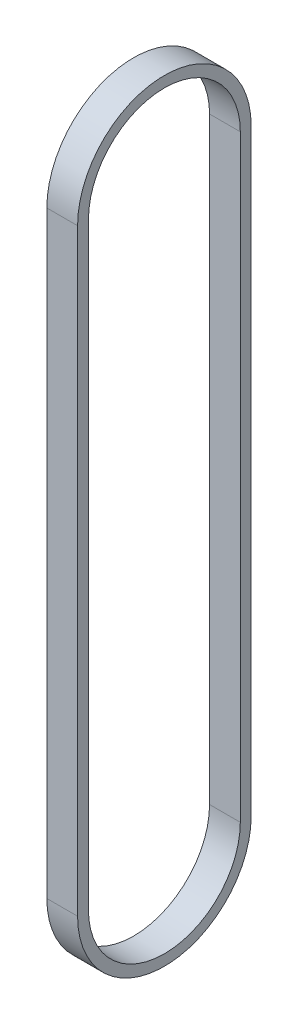
SolidWorks part; units mm, degrees
material "NEOPRENE"
ref_plane "Front Plane" through (0, 0, 0) normal (0, 0, 1) x (1, 0, 0)
ref_plane "Top Plane" through (0, 0, 0) normal (0, 1, 0) x (1, 0, 0)
ref_plane "Right Plane" through (0, 0, 0) normal (1, 0, 0) x (0, 0, -1)
sketch "Sketch1" plane through (0, 0, 0) normal (1, 0, 0) x (0, 0, -1)
  line L0 (-25.4, 0) -> (-25.4, 175.0238)
  line L1 (25.4, 175.0238) -> (25.4, 0)
  line L2 (22.225, 175.0238) -> (22.225, 0)
  line L3 (-22.225, 0) -> (-22.225, 175.0238)
  arc A0 (-25.4, 175.0238) -> (25.4, 175.0238) centre (0, 175.0238) cw
  arc A1 (-25.4, 0) -> (25.4, 0) centre (0, 0) ccw
  arc A2 (-22.225, 0) -> (22.225, 0) centre (0, 0) ccw
  arc A3 (-22.225, 175.0238) -> (22.225, 175.0238) centre (0, 175.0238) cw
  dimension "D1" = 25.4
  dimension "D2" = 175.0238
  dimension "D3" = 3.175
extrude "Boss-Extrude1" add sketch "Sketch1" along normal blind 9
